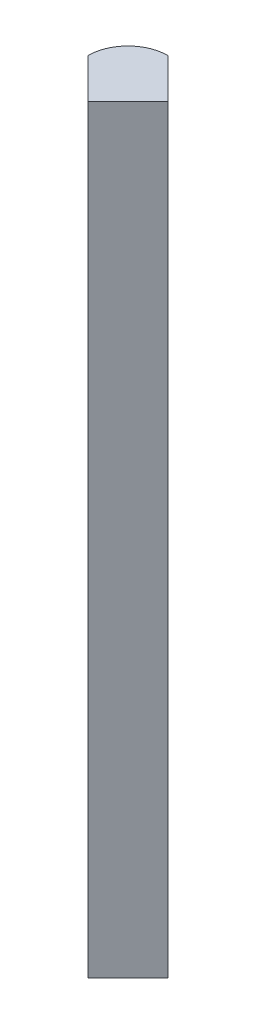
SolidWorks part; units mm, degrees
ref_plane "Front Plane" through (0, 0, 0) normal (0, 0, 1) x (1, 0, 0)
ref_plane "Top Plane" through (0, 0, 0) normal (0, 1, 0) x (1, 0, 0)
ref_plane "Right Plane" through (0, 0, 0) normal (1, 0, 0) x (0, 0, -1)
sketch "Sketch1" plane through (0, 0, 0) normal (0, 1, 0) x (1, 0, 0)
  line L2 (-4, 0.0045) -> (0, -3.9955)
  line L8 (0, -3.9955) -> (4, 0.0044)
  line L9 (0.0045, 4) -> (4, 0.0044)
  arc A3 (-4, 0.0045) -> (0.0045, 4) centre (0, 0) cw
extrude "Boss-Extrude2" add sketch "Sketch1" along normal blind 76.2
